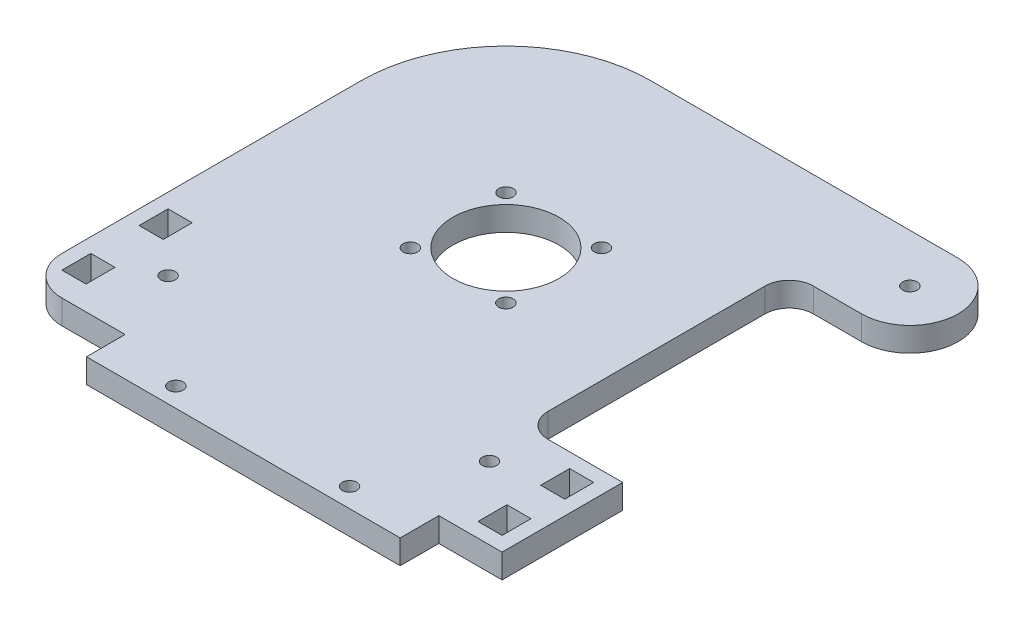
SolidWorks part; units mm, degrees
ref_plane "Front Plane" through (0, 0, 0) normal (0, 0, 1) x (1, 0, 0)
ref_plane "Top Plane" through (0, 0, 0) normal (0, 1, 0) x (1, 0, 0)
ref_plane "Right Plane" through (0, 0, 0) normal (1, 0, 0) x (0, 0, -1)
sketch "Sketch1" plane through (0, 0, 0) normal (0, 1, 0) x (1, 0, 0)
  line L0 (48.7, 25) -> (38.7, 25)
  line L1 (33.7, 20) -> (33.7, -25)
  line L2 (54.2, -30) -> (54.2, -55)
  line L3 (54.2, -55) -> (41.1, -55)
  line L4 (-45, -47.0008) -> (-45, 15.0011)
  line L5 (-15.0011, 45) -> (48.7, 45)
  line L7 (-23.9, -55) -> (-23.9, -63)
  line L8 (-23.9, -63) -> (41.1, -63)
  line L9 (41.1, -63) -> (41.1, -55)
  line L10 (-23.9, -55) -> (-37.0004, -55)
  line L11 (38.7, -30) -> (54.2, -30)
  line L12 (-42, -28) -> (-37, -28)
  line L13 (-42, -44) -> (-37, -44)
  line L14 (-42, -44) -> (-42, -50)
  line L15 (-42, -50) -> (-37, -50)
  line L16 (-37, -44) -> (-37, -50)
  line L17 (-39.5, -50) -> (-39.5, -44) construction
  line L18 (-42, -47) -> (-37, -47) construction
  line L19 (-42, -28) -> (-42, -34)
  line L20 (-42, -34) -> (-37, -34)
  line L21 (-37, -28) -> (-37, -34)
  line L22 (-39.5, -34) -> (-39.5, -28) construction
  line L23 (-42, -31) -> (-37, -31) construction
  line L24 (46.2, -33) -> (51.2, -33)
  line L25 (46.2, -46) -> (51.2, -46)
  line L26 (46.2, -46) -> (46.2, -52)
  line L27 (46.2, -52) -> (51.2, -52)
  line L28 (51.2, -46) -> (51.2, -52)
  line L29 (48.7, -52) -> (48.7, -46) construction
  line L30 (46.2, -49) -> (51.2, -49) construction
  line L31 (46.2, -33) -> (46.2, -39)
  line L32 (46.2, -39) -> (51.2, -39)
  line L33 (51.2, -33) -> (51.2, -39)
  line L34 (48.7, -39) -> (48.7, -33) construction
  line L35 (46.2, -36) -> (51.2, -36) construction
  circle A2 centre (0, 0) radius 11
  circle A7 centre (0, 0) radius 14 construction
  arc A8 (48.7, 25) -> (48.7, 45) centre (48.7, 35) ccw
  circle A14 centre (9.8929, 9.9061) radius 1.5
  circle A15 centre (9.8929, -9.9061) radius 1.5
  circle A16 centre (-9.8929, -9.9061) radius 1.5
  circle A17 centre (-9.8929, 9.9061) radius 1.5
  circle A18 centre (-9.4, -59) radius 1.5
  circle A19 centre (26.6, -59) radius 1.5
  arc A20 (-45, -47.0008) -> (-37.0004, -55) centre (-37.0004, -47.0004) ccw
  arc A21 (-45, 15.0011) -> (-15.0011, 45) centre (-15.0011, 15.0011) cw
  circle A22 centre (48.7, 35) radius 1.5
  circle A25 centre (-30, -40) radius 1.5
  circle A26 centre (36.6, -40) radius 1.5
  arc A27 (33.7, 20) -> (38.7, 25) centre (38.7, 20) cw
  arc A28 (33.7, -25) -> (38.7, -30) centre (38.7, -25) ccw
  point P48 (-39.5, -31)
  point P65 (48.7, -36)
  point P72 (48.7, -49)
  point P139 (-39.5, -47)
  dimension "D1" = 22
  dimension "D2" = 28
  dimension "D4" = 70.0011
  dimension "D5" = 3
  dimension "D6" = 13.1
  dimension "D9" = 3
  dimension "D7" = 3
  dimension "D8" = 3
  dimension "D25" = 3
  dimension "D26" = 3
  dimension "D27" = 7.9996
  dimension "D28" = 9.8929
  dimension "D30" = 90
  dimension "D31" = 29.9989
  dimension "D34" = 59.7441
  dimension "D36" = 10
  dimension "D10" = 3
  dimension "D38" = 90
  dimension "D39" = 5
  dimension "D40" = 10
  dimension "D60" = 15
  dimension "D62" = 3
  dimension "D65" = 3
  dimension "D33" = 15
  dimension "D41" = 90
  dimension "D42" = 5
  dimension "D11" = 62.002
  dimension "D12" = 21.2148
  dimension "D13" = 48.7
  dimension "D14" = 25
  dimension "D15" = 21.1
  dimension "D16" = 13.1004
  dimension "D17" = 108
  dimension "D18" = 8
  dimension "D19" = 65
  dimension "D20" = 9.8929
  dimension "D21" = 14.5
  dimension "D22" = 36
  dimension "D23" = 4
  dimension "D24" = 9.9061
  dimension "D29" = 59.8169
  dimension "D32" = 9.9061
  dimension "D35" = 48.7
  dimension "D37" = 20.5
  dimension "D43" = 15.5
  dimension "D44" = 6
  dimension "D45" = 5
  dimension "D46" = 6
  dimension "D47" = 5
  dimension "D48" = 10
  dimension "D49" = 6
  dimension "D50" = 5
  dimension "D51" = 6
  dimension "D52" = 5
  dimension "D53" = 7
  dimension "D54" = 5
  dimension "D55" = 3
  dimension "D56" = 3
  dimension "D57" = 3
  dimension "D58" = 3
  dimension "D59" = 3
  dimension "D61" = 15
  dimension "D63" = 66.6
  dimension "D64" = 15
extrude "Boss-Extrude1" add sketch "Sketch1" along normal blind 5
